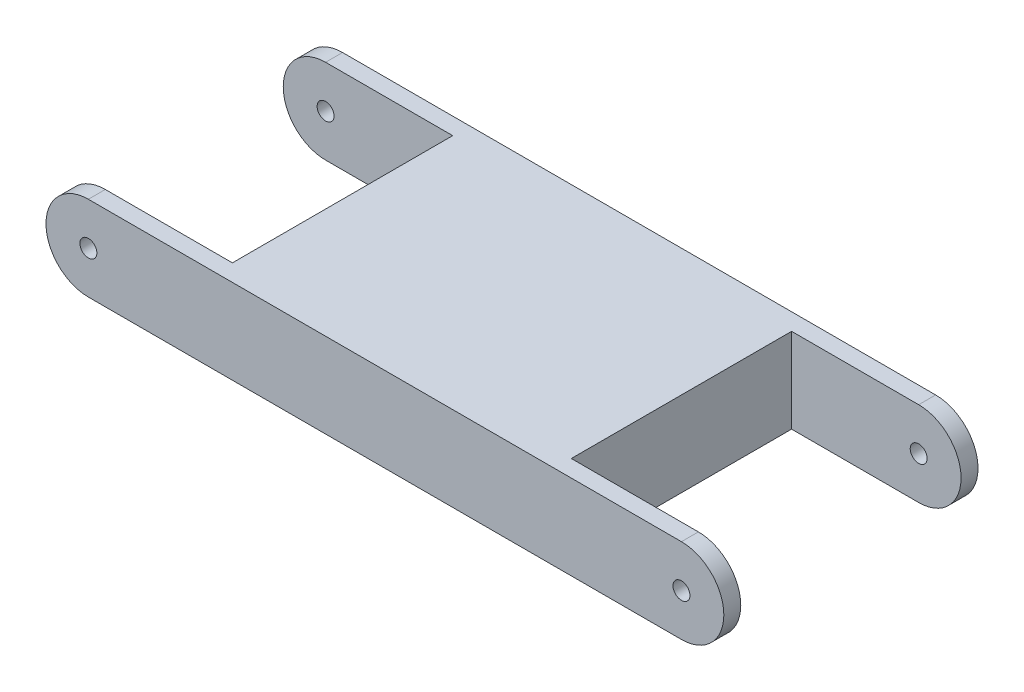
SolidWorks part; units mm, degrees
ref_plane "前基準面" through (0, 0, 0) normal (0, 0, 1) x (1, 0, 0)
ref_plane "上基準面" through (0, 0, 0) normal (0, 1, 0) x (1, 0, 0)
ref_plane "右基準面" through (0, 0, 0) normal (1, 0, 0) x (0, 0, -1)
sketch "草圖1" plane through (0, 0, 0) normal (0, 0, 1) x (1, 0, 0)
  line L0 (0, 47.1991) -> (0, -46.8309) construction
  line L1 (-71.1827, 0) -> (68.2665, 0) construction
  line L2 (-35, 0) -> (35, 0) construction
  line L3 (-35, 5) -> (35, 5)
  line L4 (-35, -5) -> (35, -5)
  arc A0 (-35, 5) -> (-35, -5) centre (-35, 0) ccw
  arc A1 (35, -5) -> (35, 5) centre (35, 0) ccw
  point P7 (0, 0)
  point P12 (0, 0)
  dimension "D2" = 5
  dimension "D1" = 70
extrude "填料-伸長1" add sketch "草圖1" along normal blind 30
sketch "草圖2" plane through (0, 0, 0) normal (0, 0, 1) x (1, 0, 0)
  line L0 (-45.1846, 0) -> (43.8227, 0) construction
  line L1 (0, 28.0802) -> (0, -27.5995) construction
  circle A0 centre (-35, 0) radius 1
  circle A1 centre (35, 0) radius 1
  dimension "D1" = 2
extrude "除料-伸長4" cut sketch "草圖2" against normal blind 30 and the other way through all
sketch "草圖3" plane through (0, 0, 0) normal (0, 1, 0) x (1, 0, 0)
  line L0 (35, 0) -> (-35, 0) construction
  line L1 (-40, -2) -> (-20, -2)
  line L2 (-40, -2) -> (-40, -28)
  line L3 (-40, -28) -> (-20, -28)
  line L4 (-20, -2) -> (-20, -28)
  line L5 (-35, -30) -> (-35, 0) construction
  line L6 (0, 16.8532) -> (0, -37.2241) construction
  line L7 (20, -2) -> (20, -28)
  line L8 (40, -28) -> (20, -28)
  line L9 (40, -2) -> (40, -28)
  line L10 (40, -2) -> (20, -2)
  dimension "D1" = 20
  dimension "D2" = 26
  dimension "D3" = 2
  dimension "D4" = 15
extrude "除料-伸長5" cut sketch "草圖3" against normal blind 30 and the other way blind 30
